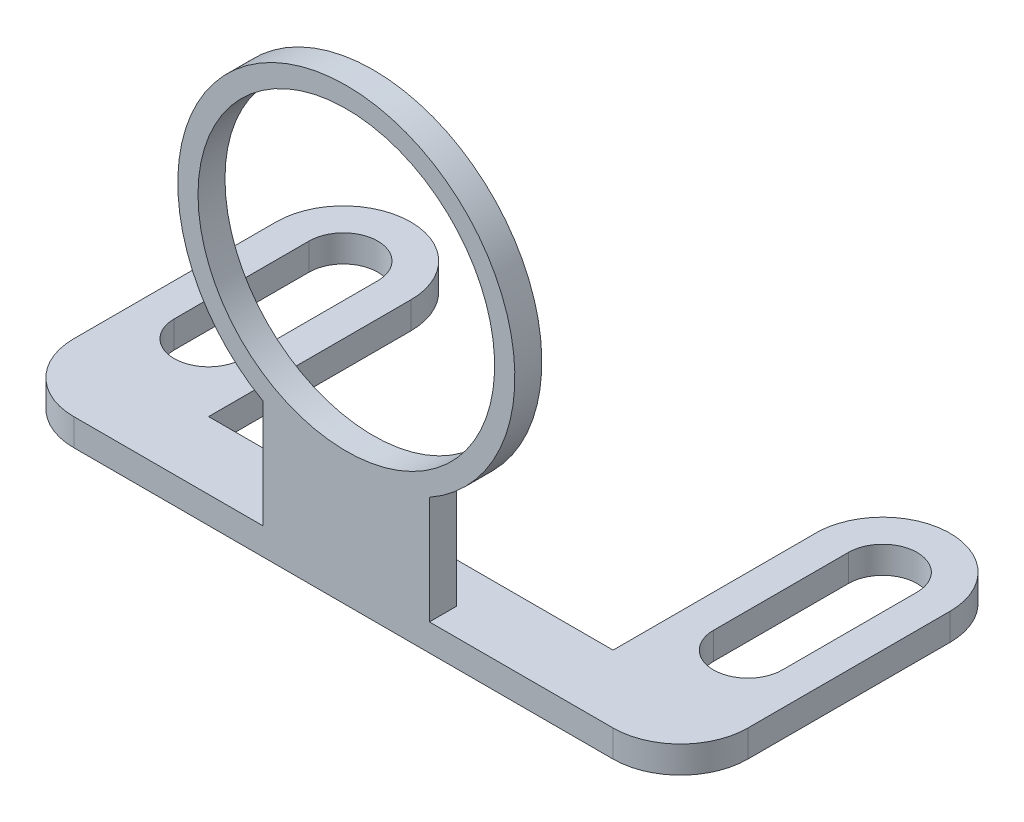
SolidWorks part; units mm, degrees
ref_plane "Front Plane" through (0, 0, 0) normal (0, 0, 1) x (1, 0, 0)
ref_plane "Top Plane" through (0, 0, 0) normal (0, 1, 0) x (1, 0, 0)
ref_plane "Right Plane" through (0, 0, 0) normal (1, 0, 0) x (0, 0, -1)
sketch "Sketch1" plane through (0, 0, 0) normal (0, 1, 0) x (1, 0, 0)
  line L0 (-50.6754, 10) -> (-50.6754, 25)
  line L1 (-25.6754, 42.4425) -> (-25.6754, -15.325) construction
  line L2 (-40.6754, 25) -> (-40.6754, 10)
  line L3 (-40.6754, 10) -> (-10.6754, 10)
  line L4 (-10.6754, 10) -> (-10.6754, 24.667)
  line L6 (-0.6754, 25) -> (-0.6754, 10)
  line L7 (-5.6754, 5) -> (-45.6754, 5)
  line L8 (-45.6754, 25) -> (-45.6754, 15) construction
  line L9 (-43.1254, 25) -> (-43.1254, 15)
  line L10 (-48.2254, 25) -> (-48.2254, 15)
  line L11 (-5.6754, 25) -> (-5.6754, 15) construction
  line L12 (-8.2254, 25) -> (-8.2254, 15)
  line L13 (-3.1254, 25) -> (-3.1254, 15)
  arc A0 (-43.1254, 25) -> (-48.2254, 25) centre (-45.6754, 25) ccw
  arc A1 (-48.2254, 15) -> (-43.1254, 15) centre (-45.6754, 15) ccw
  arc A2 (-0.6754, 25) -> (-10.6754, 24.667) centre (-5.6809, 25) ccw
  arc A3 (-40.6754, 25) -> (-50.6754, 25) centre (-45.6754, 25) ccw
  arc A4 (-8.2254, 25) -> (-3.1254, 25) centre (-5.6754, 25) cw
  arc A5 (-3.1254, 15) -> (-8.2254, 15) centre (-5.6754, 15) cw
  arc A6 (-0.6754, 10) -> (-5.6754, 5) centre (-5.6754, 10) cw
  arc A7 (-45.6754, 5) -> (-50.6754, 10) centre (-45.6754, 10) cw
  point P10 (-45.6754, 20)
  point P24 (-5.6754, 20)
  point P31 (-0.6754, 5)
  point P34 (-50.6754, 5)
  dimension "D1" = 25
  dimension "D2" = 50
  dimension "D3" = 5
  dimension "D4" = 5
extrude "Boss-Extrude1" add sketch "Sketch1" along normal blind 2
sketch "Sketch2" plane through (0, 0, -5) normal (0, 0, -1) x (-1, 0, 0)
  line L0 (19.297, 10.0044) -> (19.297, 2)
  line L1 (40.6754, 2) -> (10.6754, 2) construction
  line L2 (31.6224, 10.0044) -> (31.6224, 2)
  line L3 (19.297, 2) -> (31.6224, 2)
  arc A0 (31.6224, 10.0044) -> (19.297, 10.0044) centre (25.4597, 20.8797) ccw
  circle A1 centre (25.4597, 20.8797) radius 11
extrude "Boss-Extrude3" add sketch "Sketch2" along normal blind 2
